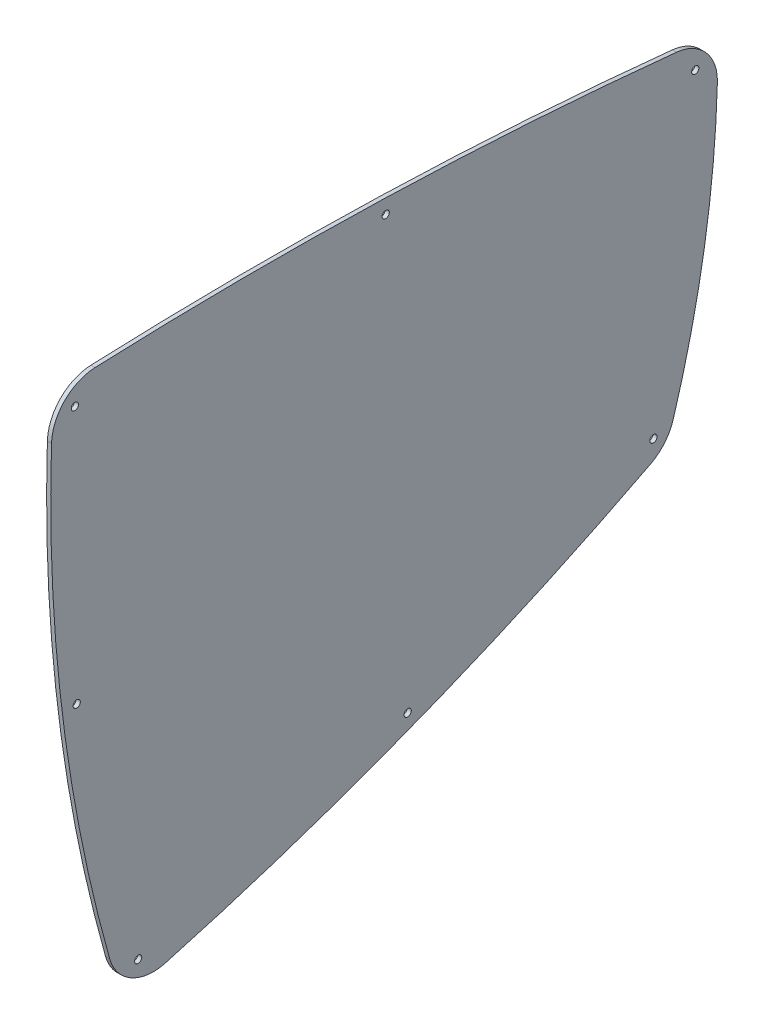
SolidWorks part; units mm, degrees
material "metacrilato"
ref_plane "Alzado" through (0, 0, 0) normal (0, 0, 1) x (1, 0, 0)
ref_plane "Planta" through (0, 0, 0) normal (0, 1, 0) x (1, 0, 0)
ref_plane "Vista lateral" through (0, 0, 0) normal (1, 0, 0) x (0, 0, -1)
sketch "Croquis2" plane through (0, 0, 0) normal (1, 0, 0) x (0, 0, -1)
  circle A8 centre (-85.886, 339.313) radius 1.75
  circle A9 centre (-235.9053, 353.6782) radius 1.75
  circle A10 centre (-386.5334, 348.4323) radius 1.75
  circle A11 centre (-385.6391, 223.1358) radius 1.75
  circle A12 centre (-355.8653, 101.0685) radius 1.75
  circle A13 centre (-225.2567, 139.2207) radius 1.75
  circle A14 centre (-106.1343, 194.691) radius 1.75
  arc A16 (-96.6141, 197.8553) -> (-75.1655, 328.8208) centre (-566.9855, 342.1285) ccw
  arc A17 (-107.5517, 184.7595) -> (-96.6141, 197.8553) centre (-117.647, 204.3065) ccw
  arc A18 (-342.6625, 92.916) -> (-107.5517, 184.7595) centre (-663.7103, 1261.6215) ccw
  arc A19 (-369.6655, 108.1631) -> (-342.6625, 92.916) centre (-348.4901, 114.1302) ccw
  arc A20 (-397.8594, 338.5678) -> (-369.6655, 108.1631) centre (363.771, 314.839) ccw
  arc A21 (-376.791, 359.8634) -> (-397.8594, 338.5678) centre (-375.8701, 337.8827) ccw
  arc A22 (-94.904, 351.3001) -> (-376.791, 359.8634) centre (-295.013, -1592.0242) ccw
  arc A23 (-75.1655, 328.8208) -> (-94.904, 351.3001) centre (-97.1575, 329.4158) ccw
  arc A24 (-96.6141, 197.8553) -> (-75.1655, 328.8208) centre (-566.9855, 342.1285) ccw
  arc A25 (-107.5517, 184.7595) -> (-96.6141, 197.8553) centre (-117.647, 204.3065) ccw
  arc A26 (-342.6625, 92.916) -> (-107.5517, 184.7595) centre (-663.7103, 1261.6215) ccw
  arc A27 (-369.6655, 108.1631) -> (-342.6625, 92.916) centre (-348.4901, 114.1302) ccw
  arc A28 (-397.8594, 338.5678) -> (-369.6655, 108.1631) centre (363.771, 314.839) ccw
  arc A29 (-376.791, 359.8634) -> (-397.8594, 338.5678) centre (-375.8701, 337.8827) ccw
  arc A30 (-94.904, 351.3001) -> (-376.791, 359.8634) centre (-295.013, -1592.0242) ccw
  arc A31 (-75.1655, 328.8208) -> (-94.904, 351.3001) centre (-97.1575, 329.4158) ccw
  dimension "D2" = 3.5
  dimension "D1" = 12
extrude "Saliente-Extruir1" add sketch "Croquis2" along normal blind 2
